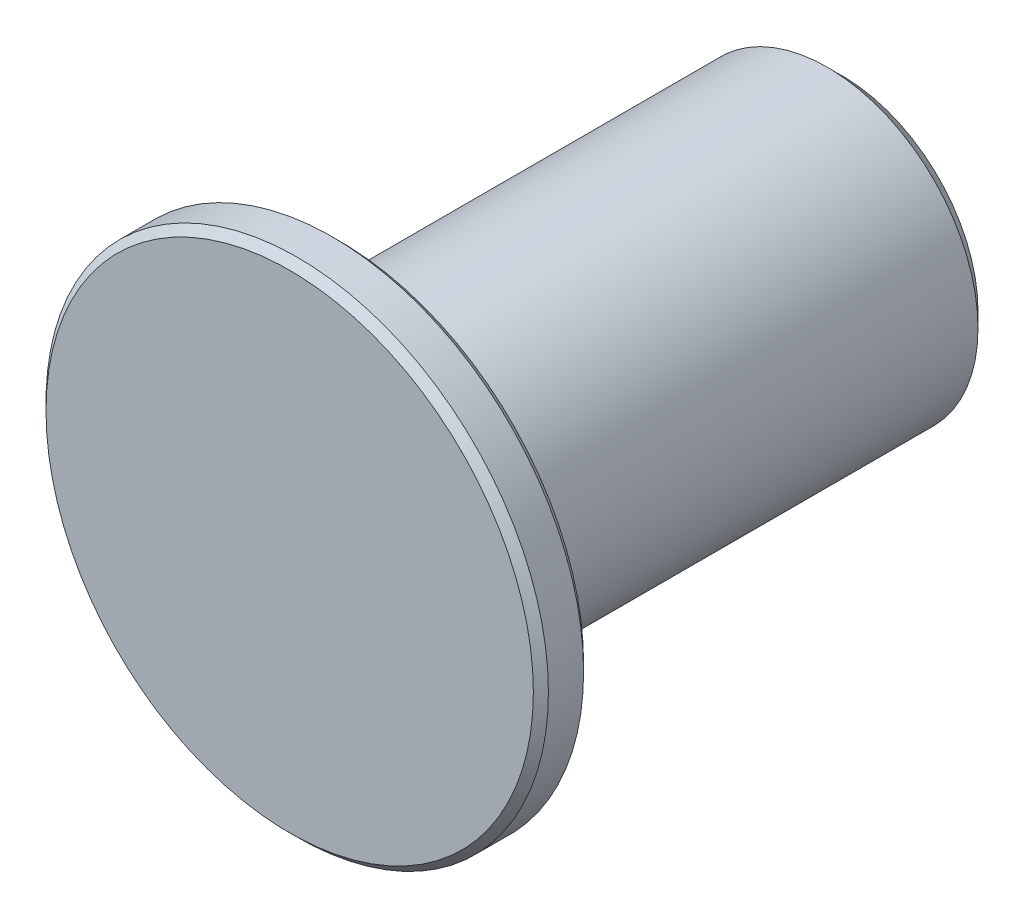
SolidWorks part; units mm, degrees
ref_plane "Front Plane" through (0, 0, 0) normal (0, 0, 1) x (1, 0, 0)
ref_plane "Top Plane" through (0, 0, 0) normal (0, 1, 0) x (1, 0, 0)
ref_plane "Right Plane" through (0, 0, 0) normal (1, 0, 0) x (0, 0, -1)
sketch "Sketch2" plane through (0, 0, 0) normal (0, 0, 1) x (1, 0, 0)
  circle A0 centre (0, 0) radius 6
  dimension "D1" = 12
extrude "Boss-Extrude1" add sketch "Sketch2" along normal blind 20
sketch "Sketch3" plane through (0, 0, 20) normal (0, 0, 1) x (1, 0, 0)
  circle A0 centre (0, 0) radius 10
  dimension "D1" = 20
extrude "Boss-Extrude2" add sketch "Sketch3" along normal blind 2
chamfer "Chamfer1" distance 0.6 angle 45 1 edges at (6, 0, 0)
chamfer "Chamfer2" distance 0.3 angle 45 2 edges at (10, 0, 20) (10, 0, 22)
